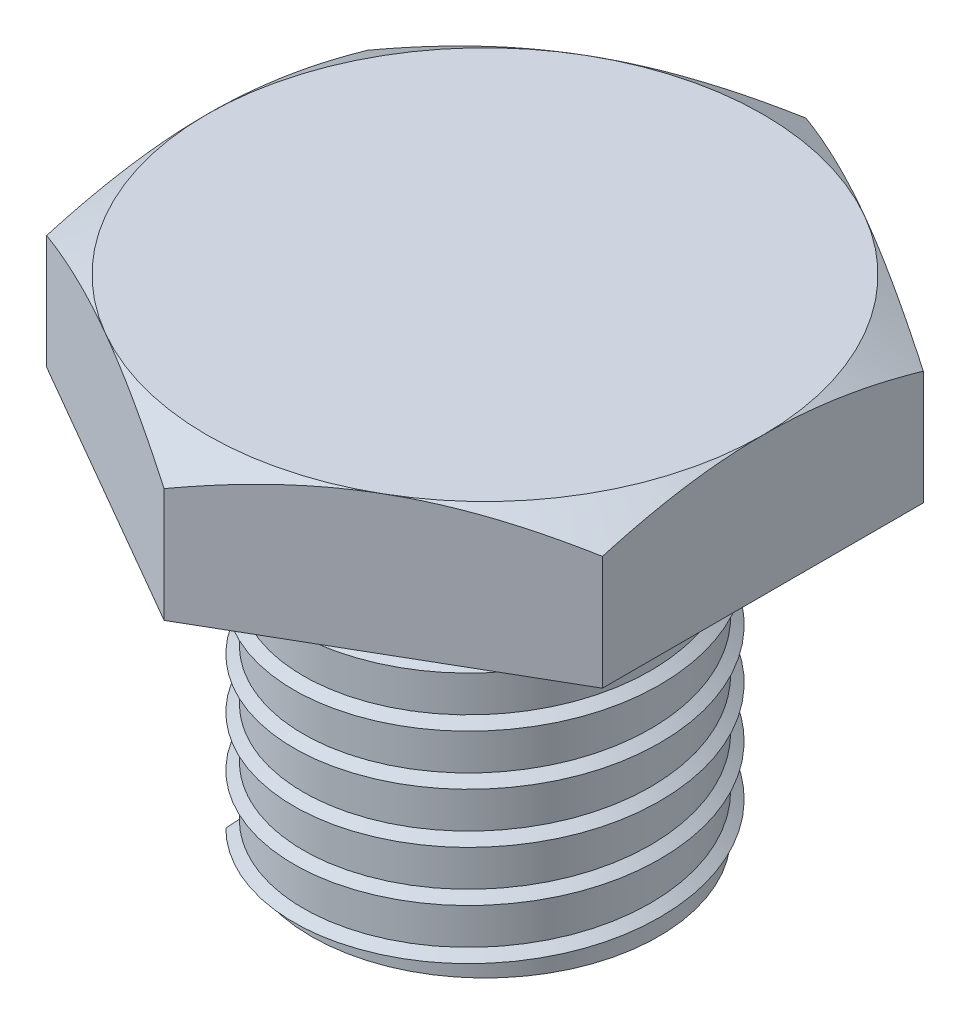
SolidWorks part; units mm, degrees
ref_plane "Alzado" through (0, 0, 0) normal (0, 0, 1) x (1, 0, 0)
ref_plane "Planta" through (0, 0, 0) normal (0, 1, 0) x (1, 0, 0)
ref_plane "Vista lateral" through (0, 0, 0) normal (1, 0, 0) x (0, 0, -1)
sketch "Croquis1" plane through (0, 0, 0) normal (0, 1, 0) x (1, 0, 0)
  line L1 (0, 11.7318) -> (-10.16, 5.8659)
  line L2 (-10.16, 5.8659) -> (-10.16, -5.8659)
  line L3 (-10.16, -5.8659) -> (0, -11.7318)
  line L4 (0, -11.7318) -> (10.16, -5.8659)
  line L5 (10.16, -5.8659) -> (10.16, 5.8659)
  line L6 (10.16, 5.8659) -> (0, 11.7318)
  circle A0 centre (0, 0) radius 10.16 construction
  dimension "D2" = 20.32
extrude "Saliente-Extruir1" add sketch "Croquis1" along normal blind 5.08
sketch "Croquis2" plane through (0, 5.08, 0) normal (0, 1, 0) x (1, 0, 0)
  circle A0 centre (0, 0) radius 10.16
extrude "Cortar-Extruir1" cut sketch "Croquis2" against normal blind 1.27 draft 60 flip side to cut
sketch "Croquis3" plane through (0, 0, 0) normal (0, -1, 0) x (1, 0, 0)
  circle A0 centre (0, 0) radius 6.35
  dimension "D1" = 12.7
extrude "Saliente-Extruir2" add sketch "Croquis3" along normal blind 12.7
sketch "Croquis4" plane through (0, -12.7, 0) normal (0, -1, 0) x (1, 0, 0)
  circle A0 centre (0, 0) radius 6.35
curve "Hélice/Espiral1" pitch 1.84 height 10.12 turns 5.5
ref_plane "Plano1" through (4.4901, -2.58, -4.4901) normal (-0.7064, 0.0461, -0.7064) x (-0.7049, 0.046, 0.7079)
sketch "Croquis5" plane through (4.4901, -2.58, -4.4901) normal (-0.7064, 0.0461, -0.7064) x (-0.7049, 0.046, 0.7079)
  line L0 (0.0006, 0.0134) -> (0.024, 0.5214)
  line L2 (0.1186, 2.5745) -> (-0.4652, -10.0985) construction
  line L3 (0.0006, 0.0134) -> (-0.3381, 0.2674)
  line L4 (-0.3381, 0.2674) -> (0.024, 0.5214)
  dimension "D1" = 0.508
sweep "Barrer3" add profiles "Croquis5" path "Hélice/Espiral1"
